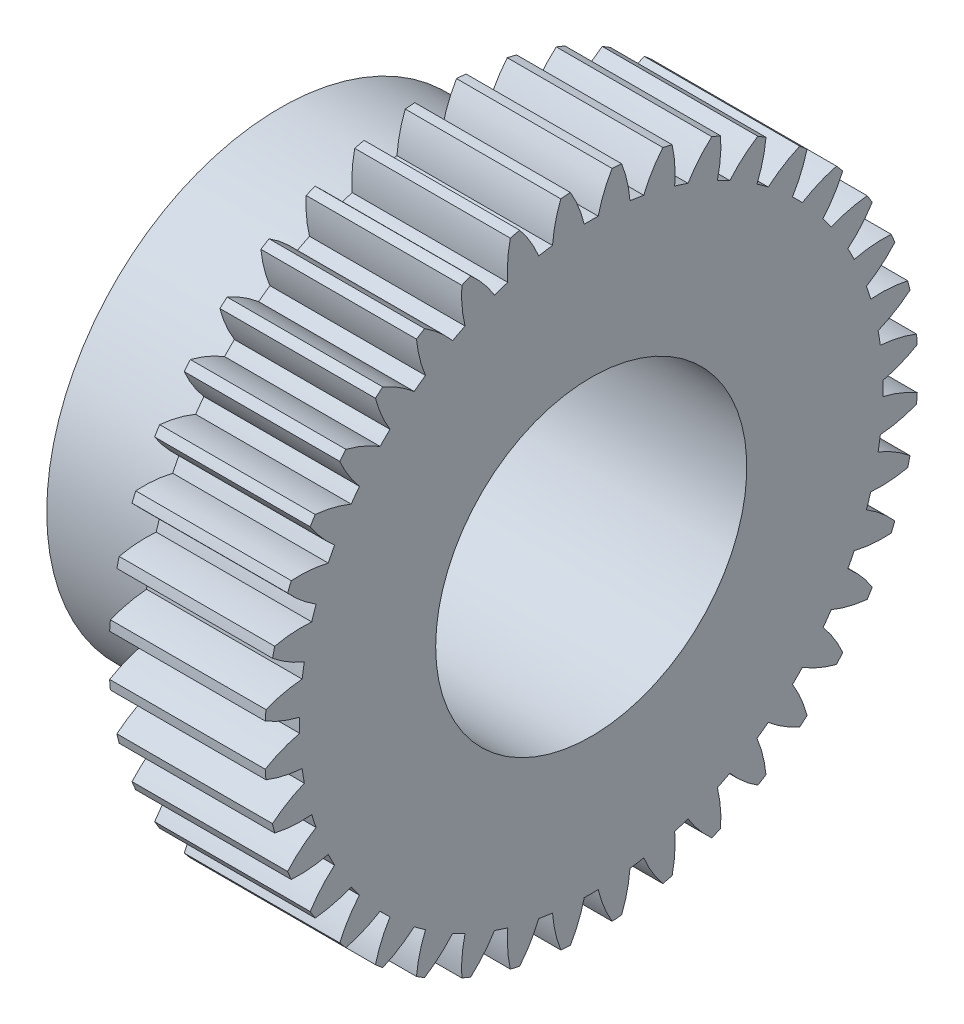
SolidWorks part; units mm, degrees
ref_plane "Plane1" through (0, 0, 0) normal (0, 0, 1) x (1, 0, 0)
ref_plane "Plane2" through (0, 0, 0) normal (0, 1, 0) x (1, 0, 0)
ref_plane "Plane3" through (0, 0, 0) normal (1, 0, 0) x (0, 0, -1)
sketch "HoldingSke" plane through (0, 0, 0) normal (0, 1, 0) x (1, 0, 0)
  line L0 (0, 0) -> (0.766, -0.6428)
  line L1 (-15, 0) -> (100, 0) construction
  line L2 (0, 0) -> (-2.1039, 2.3779)
  line L3 (0, 0) -> (-11.863, 4.5341)
  line L4 (0, 0) -> (6.6156, 5.5511)
  line L5 (0, 0) -> (-9.3695, -3.4946)
  line L6 (0, 0) -> (-8.2896, -5.593)
  line L7 (-2.1039, 2.3779) -> (0.0486, 12.1435)
  line L8 (-76.2, 54.61) -> (-73.4, 54.61)
  line L9 (-71.009, 38.7566) -> (-53.1078, 45.2721)
  line L10 (-76.2, 71.12) -> (104.1128, 71.12)
  line L11 (0, 0) -> (-10, 0)
  line L12 (-76.2, 101.6) -> (-76.162, 101.6)
  line L13 (24.9733, 27.94) -> (52.9518, 28.4284)
  line L14 (24.9733, 27.94) -> (24.9743, 27.94)
  line L15 (24.9733, 27.94) -> (100.4006, 29.5858)
  line L16 (-63.627, -1) -> (-12.827, -1)
  circle A0 centre (0, 0) radius 10
  circle A1 centre (0, 0) radius 15
  circle A2 centre (0, 0) radius 15
  circle A3 centre (0, 0) radius 10
  dimension "MHD" = 30
  dimension "Hub_dia" = 30
  dimension "Bore" = 20
  dimension "MBD" = 20
  dimension "Num_teeth" = 40
  dimension "Pitch" = 1
  dimension "Overall_len" = 10
  dimension "Show_teeth" = 40
  dimension "Thickness" = 10
  dimension "OAL" = 10.0001
  dimension "T_dim" = 2.8
  dimension "Ap" = 20
  dimension "H" = 19.05
  dimension "Pitch_radius" = 180.3128
  dimension "Width" = 10
  dimension "Backlash" = 0.038
  dimension "Addendum_fac" = 1
  dimension "Dedendum_fac" = 1.25
  dimension "Clearance_fac" = 0.25
  dimension "Dedendum_add" = 0.001
  dimension "Module" = 1
sketch "BasProSke" plane through (0, 0, 0) normal (0, 1, 0) x (1, 0, 0)
  line L0 (-10, 0) -> (60, 0) construction
  line L1 (0, 0) -> (0, 21)
  line L2 (0, 0) -> (10, 0)
  line L3 (10, 0) -> (10, 21)
  line L4 (10, 21) -> (0, 21)
  dimension "Thickness" = 10
  dimension "Diameter" = 42
revolve "Base-Revolve" add sketch "BasProSke" angle 360 about L0
sketch "TooCutSke" plane through (0, 0, 0) normal (1, 0, 0) x (0, 0, -1)
  line L1 (0, 0) -> (0, 107) construction
  line L2 (0, 0) -> (-0.8517, 19.9819) construction
  line L3 (0, 0) -> (-3.1363, 39.8509) construction
  line L4 (-0.8517, 19.9819) -> (-1.5682, 19.9255) construction
  arc A0 (0.4487, 18.7436) -> (-0.4487, 18.7436) centre (0, 0) ccw
  arc A1 (1.3547, 20.9817) -> (-1.3547, 20.9817) centre (0, 0) ccw
  circle A2 centre (0, 0) radius 20 construction
  circle A3 centre (0, 0) radius 18.7939 construction
  arc A4 (-0.4487, 18.7436) -> (-1.3547, 20.9817) centre (-8.2322, 16.895) ccw
  arc A5 (1.3547, 20.9817) -> (0.4487, 18.7436) centre (8.2322, 16.895) ccw
  dimension "Root_dia" = 37.498
  dimension "Overcut_dia" = 42.0508
  dimension "Pitch_dia" = 40
  dimension "Base_dia" = 37.5877
  dimension "Flank_rad" = 8
  dimension "Half_ang" = 4.5
  dimension "Half_CT" = 0.7187
extrude "ToothCut" cut sketch "TooCutSke" along normal through all
fillet "Breaks" [suppressed] radius 0.02
fillet "RootFillets" [suppressed] radius 0.251
pattern_circular "TeethCuts" count 40 every 9 about axis through (-10, 0, 0) along (1, 0, 0) of "ToothCut", "RootFillets", "Breaks"
sketch "HubNeaOneSke" plane through (0, 0, 0) normal (-1, 0, 0) x (0, 0, 1)
  circle A0 centre (0, 0) radius 15
  dimension "Diameter" = 30
extrude "HubNearOne" add sketch "HubNeaOneSke" along normal blind 40.0001
sketch "HubNeaBotSke" plane through (0, 0, 0) normal (-1, 0, 0) x (0, 0, 1)
  circle A0 centre (0, 0) radius 15
  dimension "Diameter" = 30
extrude "HubNearBoth" [suppressed] add sketch "HubNeaBotSke" along normal blind 20
ref_plane "FarPln" through (10, 0, 0) normal (1, 0, 0) x (0, 0, -1)
sketch "HubFarSke" plane through (10, 0, 0) normal (1, 0, 0) x (0, 0, -1)
  circle A0 centre (0, 0) radius 15
  dimension "Diameter" = 30
extrude "HubFar" [suppressed] add sketch "HubFarSke" along normal blind 20
sketch "BorSke" plane through (0, 0, 0) normal (1, 0, 0) x (0, 0, -1)
  circle A0 centre (0, 0) radius 10
  dimension "Diameter" = 20
extrude "Bore" cut sketch "BorSke" along normal mid plane 20.0001
sketch "KeySke" plane through (0, 0, 0) normal (1, 0, 0) x (0, 0, -1)
  line L0 (-3, 0) -> (-3, 12.8)
  line L1 (-3, 12.8) -> (3, 12.8)
  line L2 (3, 12.8) -> (3, 0)
  line L3 (0, 0) -> (0, 34) construction
  line L4 (-3, 0) -> (3, 0)
  dimension "Offset" = 12.8
  dimension "Width" = 6
extrude "Keyway" [suppressed] cut sketch "KeySke" along normal mid plane 20.0001
pattern_circular "Keyway2" [suppressed] count 2 every 90 about axis through (-10, 0, 0) along (1, 0, 0)
ref_plane "基准面1" through (-10, 0, 0) normal (-1, 0, 0) x (0, 0, 1)
sketch "草图1" plane through (-10, 0, 0) normal (-1, 0, 0) x (0, 0, 1)
  circle A0 centre (0, 0) radius 32.8833
extrude "切除-拉伸1" cut sketch "草图1" along normal through all
equation "' \"Module@HoldingSke\" = 6.35"
equation "' \"Num_teeth@HoldingSke\" = 12"
equation "' \"Ap@HoldingSke\" =  20"
equation "' \"Ap@HoldingSke\" = 20"
equation "' \"Width@HoldingSke\" = 0.5 * 25.4"
equation "' \"Hub_dia@HoldingSke\"= 1 * 25.4"
equation "' \"Hub_dia@HoldingSke\" = 1 * 25.4"
equation "' \"Overall_len@HoldingSke\" = 1.0 * 25.4"
equation "' \"Bore@HoldingSke\" = 0.75 * 25.4"
equation "' \"T_dim@HoldingSke\" = 0.1 * 25.4"
equation "' \"Width@KeySke\" = 0.25 * 25.4"
equation "' \"Show_teeth@HoldingSke\" = 13"
equation "' \"Backlash@HoldingSke\" = 0.009 * 25.4"
equation "' \"Addendum_fac@HoldingSke\" = 1.0"
equation "' \"Dedendum_fac@HoldingSke\" = 1.25"
equation "' \"Dedendum_add@HoldingSke\" = 0.00005 * 25.4"
equation "' \"Clearance_fac@HoldingSke\" = 0.25"
equation "\"Pitch@HoldingSke\" = 1 / \"Module@HoldingSke\""
equation "\"Overcut_dia@TooCutSke\" = (\"Num_teeth@HoldingSke\" + 2 * \"Addendum_fac@HoldingSke\") / \"Pitch@HoldingSke\" + 0.002 * 25.4"
equation "\"Pitch_dia@TooCutSke\" = \"Num_teeth@HoldingSke\" / \"Pitch@HoldingSke\""
equation "\"Base_dia@TooCutSke\" = \"Num_teeth@HoldingSke\" / \"Pitch@HoldingSke\" * cos((\"Ap@HoldingSke\"  * 3.14159265 / 180))"
equation "\"Root_dia@TooCutSke\" = (\"Num_teeth@HoldingSke\" + 2) / \"Pitch@HoldingSke\" - 2 * (\"Addendum_fac@HoldingSke\" + \"Dedendum_fac@HoldingSke\") / \"Pitch@HoldingSke\" - \"Dedendum_add@HoldingSke\" * 2"
equation "\"Half_ang@TooCutSke\" = 180 / \"Num_teeth@HoldingSke\""
equation "\"Half_CT@TooCutSke\" = \"Num_teeth@HoldingSke\" / \"Pitch@HoldingSke\" * sin((3.14159265 / 2 / \"Num_teeth@HoldingSke\")) / 2 - 7 * \"Backlash@HoldingSke\" / 4"
equation "\"Flank_rad@TooCutSke\" = \"Num_teeth@HoldingSke\" / \"Pitch@HoldingSke\" / 5"
equation "\"Radius@RootFillets\" = \"Clearance_fac@HoldingSke\" / \"Pitch@HoldingSke\" + \"Dedendum_add@HoldingSke\""
equation "\"Break_rad@Breaks\" = 0.02 / \"Pitch@HoldingSke\""
equation "\"Thickness@HoldingSke\" = \"Width@HoldingSke\""
equation "\"OAL@HoldingSke\" = \"Thickness@HoldingSke\""
equation "\"MHD@HoldingSke\" = (\"Num_teeth@HoldingSke\" + 2) / \"Pitch@HoldingSke\" - 2 * (\"Addendum_fac@HoldingSke\" + \"Dedendum_fac@HoldingSke\")  / \"Pitch@HoldingSke\" - \"Dedendum_add@HoldingSke\" * 2"
equation "\"MBD@HoldingSke\" = (\"Num_teeth@HoldingSke\" + 2) / \"Pitch@HoldingSke\" - 2 * (\"Addendum_fac@HoldingSke\" + \"Dedendum_fac@HoldingSke\")  / \"Pitch@HoldingSke\" - \"Dedendum_add@HoldingSke\" * 2 - 0.002 * 25.4"
equation "\"MHD@HoldingSke\" = ((sgn( \"MHD@HoldingSke\" - \"Hub_dia@HoldingSke\" )-1)*( \"MHD@HoldingSke\" - \"Hub_dia@HoldingSke\" ))/-2+ \"Hub_dia@HoldingSke\""
equation "\"MBD@HoldingSke\" = ((sgn( \"MBD@HoldingSke\" - \"Bore@HoldingSke\" )-1)*( \"MBD@HoldingSke\" - \"Bore@HoldingSke\" ))/-2+ \"Bore@HoldingSke\""
equation "\"OAL@HoldingSke\" = ((sgn( \"OAL@HoldingSke\" - \"Overall_len@HoldingSke\" )+1)*( \"OAL@HoldingSke\" - \"Overall_len@HoldingSke\" ))/2 + \"Overall_len@HoldingSke\" + 0.000002 * 25.4"
equation "\"Num_teeth@TeethCuts\" = int( \"Show_teeth@HoldingSke\" ) + 1"
equation "\"Num_teeth@TeethCuts\" = ((sgn( \"Num_teeth@TeethCuts\" - \"Num_teeth@HoldingSke\" )-1)*( \"Num_teeth@TeethCuts\" - \"Num_teeth@HoldingSke\" ))/-2+ \"Num_teeth@HoldingSke\""
equation "\"Num_teeth@TeethCuts\" = ((sgn( \"Num_teeth@TeethCuts\" - 2.0)+1)*( \"Num_teeth@TeethCuts\" - 2.0))/2 +2.0"
equation "\"Angle@TeethCuts\" = 360.0 / \"Num_teeth@HoldingSke\""
equation "\"Diameter@BasProSke\" = (\"Num_teeth@HoldingSke\" + 2 * \"Addendum_fac@HoldingSke\") / \"Pitch@HoldingSke\""
equation "\"Thickness@BasProSke\"  = \"Thickness@HoldingSke\""
equation "' \"Fillet_rad@BasProSke\" =  \"Thickness@HoldingSke\" * 0.05"
equation "' \"Fillet_rad@BasProSke\" = \"Thickness@HoldingSke\" * 0.05"
equation "\"MHD@HoldingSke\" = ((sgn( \"MHD@HoldingSke\" - \"Root_dia@TooCutSke\" )-1)*( \"MHD@HoldingSke\" - \"Root_dia@TooCutSke\" ))/-2+ \"Root_dia@TooCutSke\""
equation "\"Diameter@HubNeaOneSke\" = \"MHD@HoldingSke\""
equation "\"Length@HubNearOne\" = \"OAL@HoldingSke\" - \"Thickness@BasProSke\""
equation "\"Diameter@HubNeaBotSke\" = \"MHD@HoldingSke\""
equation "\"Length@HubNearBoth\" = ( \"OAL@HoldingSke\" - \"Thickness@BasProSke\" ) / 2.0"
equation "\"Thickness@FarPln\" = \"Thickness@BasProSke\""
equation "\"Diameter@HubFarSke\" = \"MHD@HoldingSke\""
equation "\"Length@HubFar\" = ( \"OAL@HoldingSke\" - \"Thickness@BasProSke\" ) / 2.0"
equation "\"Diameter@BorSke\" = \"MBD@HoldingSke\""
equation "\"D1@Bore\" = \"OAL@HoldingSke\" * 2.0"
equation "\"D1@Keyway\" = \"OAL@HoldingSke\" * 2.0"
equation "\"Offset@KeySke\" = \"T_dim@HoldingSke\" + \"MBD@HoldingSke\" / 2.0"
